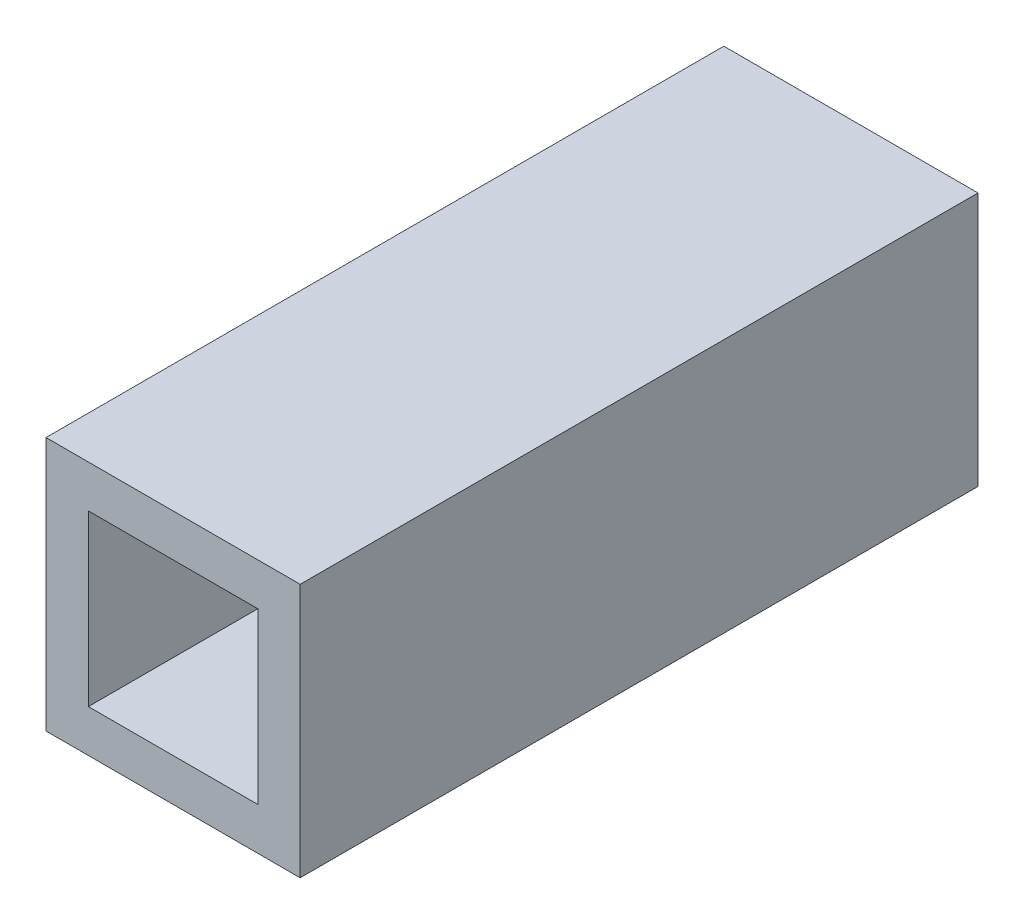
SolidWorks part; units mm, degrees
ref_plane "Front Plane" through (0, 0, 0) normal (0, 0, 1) x (1, 0, 0)
ref_plane "Top Plane" through (0, 0, 0) normal (0, 1, 0) x (1, 0, 0)
ref_plane "Right Plane" through (0, 0, 0) normal (1, 0, 0) x (0, 0, -1)
sketch "Sketch1" plane through (0, 0, 0) normal (0, 0, 1) x (1, 0, 0)
  line L1 (-9.525, -9.525) -> (9.525, -9.525)
  line L2 (-9.525, -9.525) -> (-9.525, 9.525)
  line L3 (-9.525, 9.525) -> (9.525, 9.525)
  line L4 (9.525, -9.525) -> (9.525, 9.525)
  line L5 (-9.525, -9.525) -> (9.525, 9.525) construction
  line L6 (-9.525, 9.525) -> (9.525, -9.525) construction
  point P0 (0, 0)
  dimension "D1" = 19.05
  dimension "D2" = 19.05
extrude "Boss-Extrude1" add sketch "Sketch1" against normal blind 50.8
sketch "Sketch2" plane through (0, 0, 0) normal (0, 0, 1) x (1, 0, 0)
  line L1 (-6.35, -6.35) -> (6.35, -6.35)
  line L2 (-6.35, -6.35) -> (-6.35, 6.35)
  line L3 (-6.35, 6.35) -> (6.35, 6.35)
  line L4 (6.35, -6.35) -> (6.35, 6.35)
  line L5 (-6.35, -6.35) -> (6.35, 6.35) construction
  line L6 (-6.35, 6.35) -> (6.35, -6.35) construction
  point P0 (0, 0)
  dimension "D1" = 12.7
  dimension "D2" = 12.7
extrude "Cut-Extrude1" cut sketch "Sketch2" against normal up to next
equation "\"D2@Sketch1\"=\"D1@Sketch1\""
equation "\"D2@Sketch2\"=\"D1@Sketch2\""
